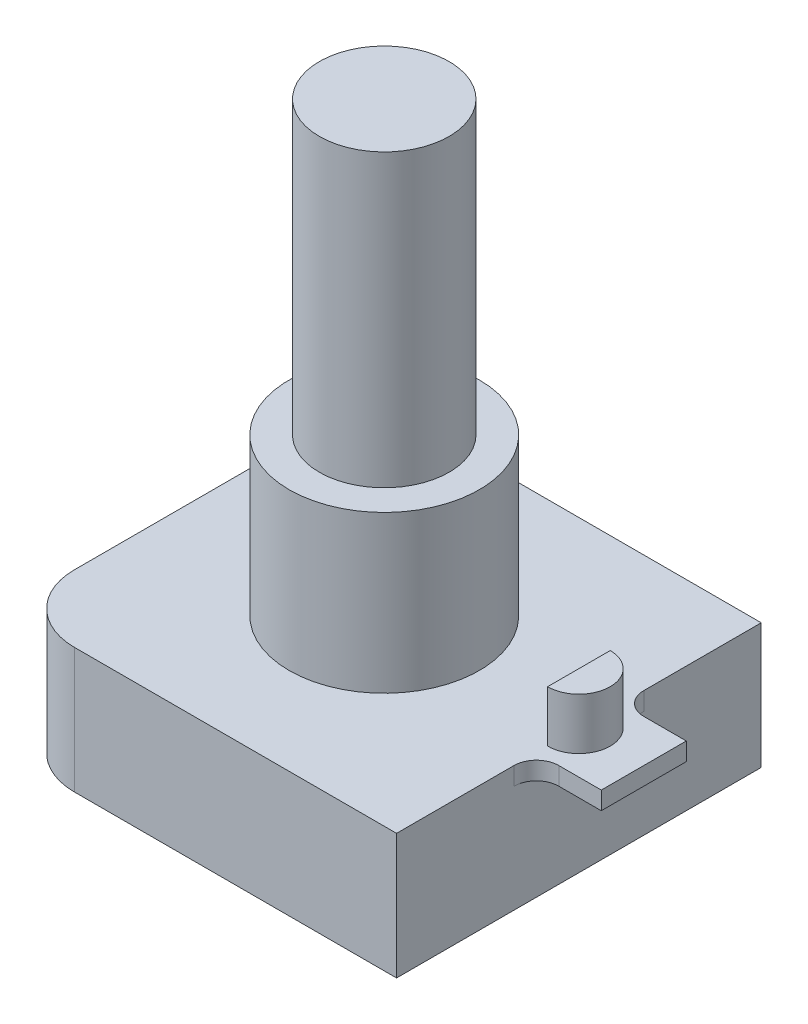
SolidWorks part; units mm, degrees
ref_plane "Спереди" through (0, 0, 0) normal (0, 0, 1) x (1, 0, 0)
ref_plane "Сверху" through (0, 0, 0) normal (0, 1, 0) x (1, 0, 0)
ref_plane "Справа" through (0, 0, 0) normal (1, 0, 0) x (0, 0, -1)
sketch "Sketch1" plane through (0, 0, 0) normal (0, 1, 0) x (1, 0, 0)
  line L1 (8.7, -8.15) -> (-8.7, -8.15)
  line L2 (8.7, -8.15) -> (8.7, 8.15)
  line L3 (8.7, 8.15) -> (-8.7, 8.15)
  line L4 (-8.7, -8.15) -> (-8.7, 8.15)
  line L5 (8.7, -8.15) -> (-8.7, 8.15) construction
  line L6 (8.7, 8.15) -> (-8.7, -8.15) construction
  point P0 (0, 0)
  dimension "D1" = 16.3
  dimension "D2" = 17.4
extrude "Boss-Extrude1" add sketch "Sketch1" along normal blind 5.6
sketch "Sketch2" plane through (0, 5.6, 0) normal (0, 1, 0) x (1, 0, 0)
  circle A0 centre (0, 0) radius 4.25
  dimension "D1" = 8.5
extrude "Boss-Extrude2" add sketch "Sketch2" along normal blind 7
sketch "Sketch3" plane through (0, 12.6, 0) normal (0, 1, 0) x (1, 0, 0)
  circle A0 centre (0, 0) radius 2.9
  dimension "D1" = 5.8
extrude "Boss-Extrude3" add sketch "Sketch3" along normal blind 13
fillet "Fillet1" radius 3 2 edges at (-8.7, 2.8, -8.15) (-8.7, 2.8, 8.15)
sketch "Sketch4" plane through (8.7, 0, 0) normal (1, 0, 0) x (0, 0, -1)
  line L0 (8.15, 5.2) -> (-8.15, 5.2) construction
  line L1 (8.15, 5.6) -> (8.15, 0) construction
  line L2 (-8.15, 5.6) -> (-8.15, 0) construction
  line L3 (-8.15, 5.6) -> (8.15, 5.6) construction
  line L4 (-1.9, 4.8) -> (1.9, 4.8)
  line L5 (-1.9, 4.8) -> (-1.9, 5.6)
  line L6 (-1.9, 5.6) -> (1.9, 5.6)
  line L7 (1.9, 4.8) -> (1.9, 5.6)
  line L8 (-1.9, 4.8) -> (1.9, 5.6) construction
  line L9 (-1.9, 5.6) -> (1.9, 4.8) construction
  point P6 (0, 5.2)
  dimension "D1" = 3.8
  dimension "D2" = 0.8
extrude "Boss-Extrude4" add sketch "Sketch4" along normal blind 2.9
fillet "Fillet2" radius 1 2 edges at (8.7, 5.2, -1.9) (8.7, 5.2, 1.9)
sketch "Sketch5" plane through (0, 5.6, 0) normal (0, 1, 0) x (1, 0, 0)
  line L0 (8.7, 8.15) -> (8.7, -8.15) construction
  line L1 (8.7, 1.4) -> (8.7, -1.4)
  arc A0 (8.7, -1.4) -> (8.7, 1.4) centre (8.7, 0) ccw
  point P9 (8.7, 0)
  dimension "D1" = 1.4
extrude "Boss-Extrude5" add sketch "Sketch5" along normal blind 2.3
